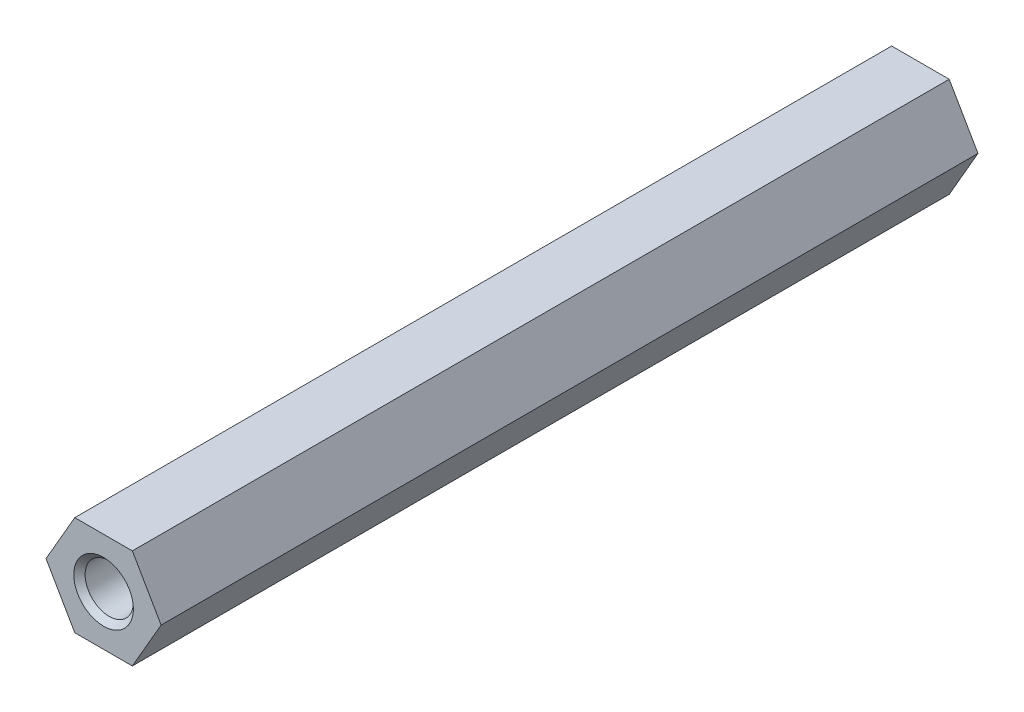
SolidWorks part; units mm, degrees
material "6061 Alloy"
ref_plane "Front Plane" through (0, 0, 0) normal (0, 0, 1) x (1, 0, 0)
ref_plane "Top Plane" through (0, 0, 0) normal (0, 1, 0) x (1, 0, 0)
ref_plane "Right Plane" through (0, 0, 0) normal (1, 0, 0) x (0, 0, -1)
sketch "Sketch1" plane through (0, 0, 0) normal (0, 0, 1) x (1, 0, 0)
  line L1 (3.5796, 0) -> (1.7898, 3.1)
  line L2 (1.7898, 3.1) -> (-1.7898, 3.1)
  line L3 (-1.7898, 3.1) -> (-3.5796, 0)
  line L4 (-3.5796, 0) -> (-1.7898, -3.1)
  line L5 (-1.7898, -3.1) -> (1.7898, -3.1)
  line L6 (1.7898, -3.1) -> (3.5796, 0)
  circle A0 centre (0, 0) radius 3.1 construction
extrude "Extrude1" add sketch "Sketch1" against normal blind 50.8
hole_wizard "#6-32 Tapped Hole8" positions "3DSketch13" profile "Sketch27" tap size "#6-32" standard "Ansi Inch" end condition through all
sketch3d "3DSketch13"
  point P0 (0.0004, 0.0007, 0)
  dimension "D1" = 3.58
  dimension "D2" = 3.58
sketch "Sketch27" plane through (0.0004, 0.0007, 0) normal (1, 0, 0) x (0, -1, 0)
  line L0 (0, 0) -> (0, 50.8)
  line L1 (0, 50.8) -> (1.3525, 50.8)
  line L2 (1.3525, 50.8) -> (1.3525, 0)
  line L5 (1.3525, 0) -> (0, 0)
  line L11 (0, -6.35) -> (0, 107.95) construction
  dimension "Thru Tap Drill Dia." = 2.7051
  dimension "Thru Tap Drill Depth" = 50.8
cosmetic thread "Hole Thread12" parameters "D2"=3.5052
chamfer "Chamfer1" distance 0.5 angle 45 1 edges at (1.353, 0.0007, 0)
chamfer "Chamfer2" distance 0.5 angle 45 1 edges at (1.353, 0.0007, -50.8)
sketch "Sketch15" plane through (0, 0, 0) normal (0, 0, 1) x (1, 0, 0)
  circle A0 centre (0, 0) radius 1.5
  dimension "D1" = 3
extrude "Cut-Extrude1" cut sketch "Sketch15" against normal through all
